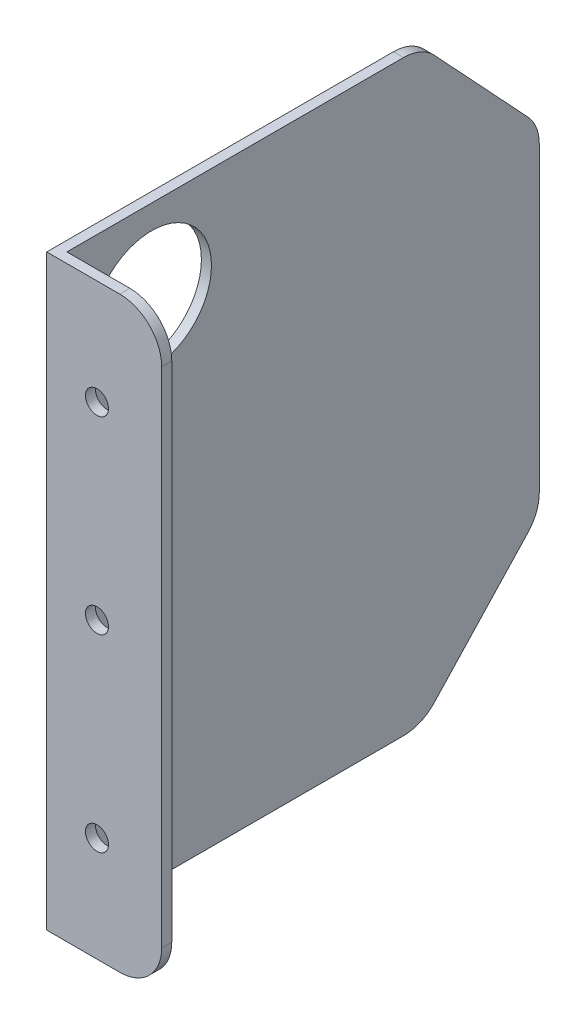
SolidWorks part; units mm, degrees
ref_plane "Front Plane" through (0, 0, 0) normal (0, 0, 1) x (1, 0, 0)
ref_plane "Top Plane" through (0, 0, 0) normal (0, 1, 0) x (1, 0, 0)
ref_plane "Right Plane" through (0, 0, 0) normal (1, 0, 0) x (0, 0, -1)
sketch "Sketch1" plane through (0, 0, 0) normal (1, 0, 0) x (0, 0, -1)
  line L1 (0, 0) -> (115, 0)
  line L2 (0, 0) -> (0, -140)
  line L3 (0, -140) -> (115, -140)
  line L4 (115, 0) -> (115, -140)
  dimension "D1" = 115
  dimension "D2" = 140
extrude "Boss-Extrude1" add sketch "Sketch1" along normal blind 2.4
sketch "Sketch2" plane through (2.4, 0, 0) normal (1, 0, 0) x (0, 0, -1)
  line L0 (87, 0) -> (115, -30)
  line L1 (115, 0) -> (0, 0) construction
  line L2 (115, -140) -> (115, 0) construction
  line L3 (115, -30) -> (142.6162, -32.5054)
  line L4 (142.6162, -32.5054) -> (142.6162, 14.8756)
  line L5 (142.6162, 14.8756) -> (87, 0)
  line L6 (115, -110) -> (87, -140)
  line L7 (0, -140) -> (115, -140) construction
  line L8 (87, -140) -> (87, -152.6611)
  line L9 (87, -152.6611) -> (136.31, -152.6611)
  line L10 (136.31, -152.6611) -> (115, -110)
  line L12 (0, 0) -> (0, -140) construction
  dimension "D1" = 30
  dimension "D2" = 87
  dimension "D3" = 87
  dimension "D4" = 30
extrude "Cut-Extrude1" cut sketch "Sketch2" against normal through all
fillet "Fillet1" radius 10 4 edges at (1.2, -140, -87) (1.2, -110, -115) (1.2, -30, -115) (1.2, 0, -87)
sketch "Sketch3" plane through (2.4, 0, 0) normal (1, 0, 0) x (0, 0, -1)
  line L0 (82.6545, 0) -> (0, 0) construction
  line L1 (0, -140) -> (2.4, -140)
  line L2 (0, -140) -> (0, 0)
  line L3 (0, 0) -> (2.4, 0)
  line L4 (2.4, -140) -> (2.4, 0)
  dimension "D1" = 2.4
extrude "Boss-Extrude2" add sketch "Sketch3" along normal blind 25
fillet "Fillet2" radius 10 2 edges at (27.4, -140, -1.2) (27.4, 0, -1.2)
sketch "Sketch4" plane through (0, 0, 0) normal (0, 0, 1) x (1, 0, 0)
  line L0 (17.4, 0) -> (0, 0) construction
  line L1 (17.4, -140) -> (0, -140) construction
  line L2 (27.4, -10) -> (27.4, -130) construction
  circle A0 centre (11.975, -70) radius 2.75
  circle A1 centre (11.975, -25) radius 2.75
  circle A2 centre (11.975, -115) radius 2.75
  point P12 (27.4, -70)
  dimension "D1" = 5.5
  dimension "D2" = 5.5
  dimension "D3" = 5.5
  dimension "D4" = 25
  dimension "D5" = 25
extrude "Cut-Extrude2" cut sketch "Sketch4" against normal through all
sketch "Sketch5" plane through (2.4, 0, 0) normal (1, 0, 0) x (0, 0, -1)
  line L0 (82.6545, 0) -> (2.4, 0) construction
  circle A0 centre (22.5917, -20) radius 14.275
  dimension "D2" = 28.55
  dimension "D1" = 20
extrude "Cut-Extrude3" cut sketch "Sketch5" against normal through all
